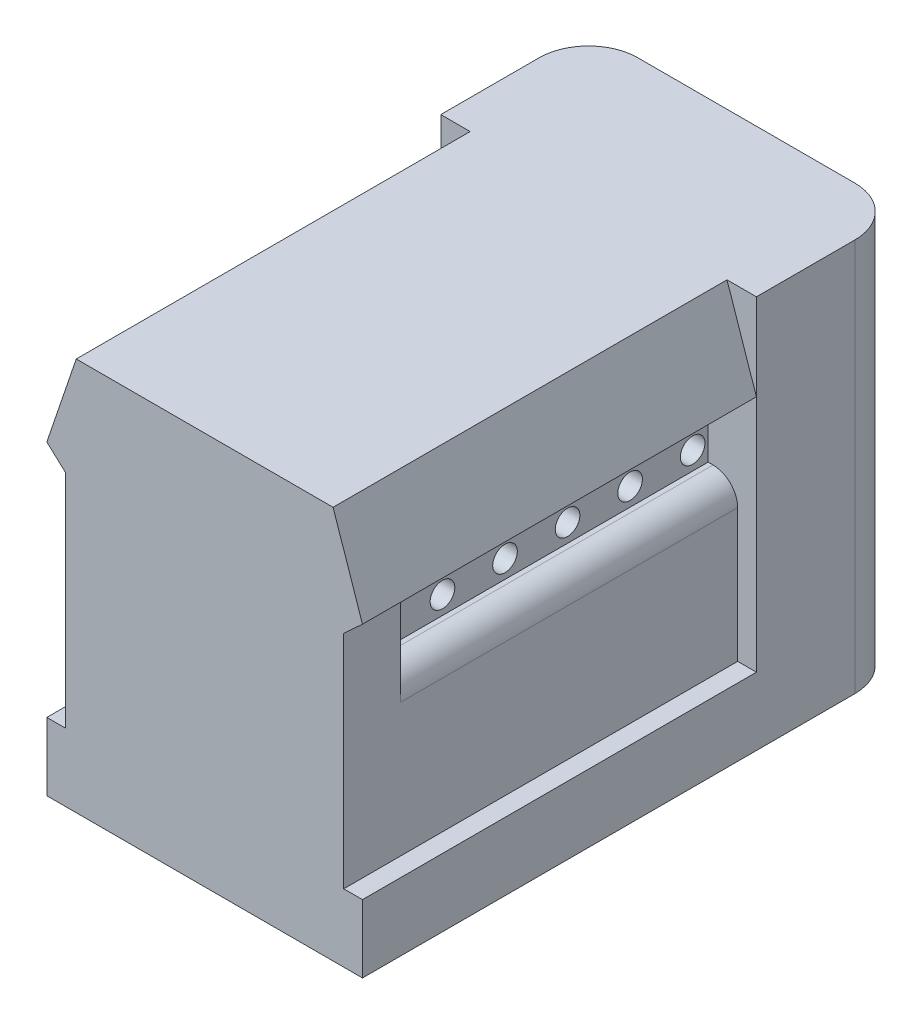
SolidWorks part; units mm, degrees
ref_plane "Plan de face" through (0, 0, 0) normal (0, 0, 1) x (1, 0, 0)
ref_plane "Plan de dessus" through (0, 0, 0) normal (0, 1, 0) x (1, 0, 0)
ref_plane "Plan de droite" through (0, 0, 0) normal (1, 0, 0) x (0, 0, -1)
sketch "Esquisse1" plane through (0, 0, 0) normal (0, 0, 1) x (1, 0, 0)
  line L0 (0, 0) -> (0, 63.4039) construction
  line L1 (-4.4493, 10.641) -> (-4.4493, 9.1647)
  line L2 (-6.41, 0) -> (-6.41, 2.7566)
  line L3 (-6.41, 2.7566) -> (-5.6493, 2.7566)
  line L4 (-4.4493, 9.1647) -> (-4.6493, 9.1647)
  line L5 (-4.4493, 10.641) -> (-6.41, 12.4442)
  line L6 (-6.41, 12.4442) -> (-5.2156, 15.9609)
  line L7 (-5.6493, 8.1647) -> (-5.6493, 2.7566)
  line L8 (-5.2156, 15.9609) -> (5.2156, 15.9609)
  line L9 (0, 0) -> (-6.41, 0)
  line L10 (5.6493, 8.1647) -> (5.6493, 2.7566)
  line L11 (6.41, 12.4442) -> (5.2156, 15.9609)
  line L12 (4.4493, 10.641) -> (6.41, 12.4442)
  line L13 (4.4493, 9.1647) -> (4.6493, 9.1647)
  line L14 (6.41, 2.7566) -> (5.6493, 2.7566)
  line L15 (6.41, 0) -> (6.41, 2.7566)
  line L16 (4.4493, 10.641) -> (4.4493, 9.1647)
  line L17 (0, 0) -> (6.41, 0)
  arc A0 (-4.6493, 9.1647) -> (-5.6493, 8.1647) centre (-4.6493, 8.1647) ccw
  arc A1 (4.6493, 9.1647) -> (5.6493, 8.1647) centre (4.6493, 8.1647) cw
  point P14 (-5.6493, 9.1647)
  point P20 (0, 15.9609)
  dimension "D2" = 1
  dimension "D1" = 1.2
  dimension "D3" = 0.7607
  dimension "D4" = 5.4081
  dimension "D5" = 1.4763
  dimension "D6" = 1.8032
  dimension "D7" = 132.604
  dimension "D8" = 3.714
  dimension "D9" = 113.845
  dimension "D10" = 6.41
extrude "Extrusion1" add sketch "Esquisse1" along normal blind 16
ref_plane "Plan1" through (6.41, 0, 0) normal (1, 0, 0) x (0, 0, -1)
sketch "Esquisse2" plane through (0, 15.9609, 0) normal (0, 1, 0) x (1, 0, 0)
  line L0 (0, 0) -> (0, 6.3868) construction
  line L1 (5.2156, 0) -> (-5.2156, 0) construction
  line L2 (6.41, -7.9805) -> (6.41, 7.9805) construction
  line L4 (-6.41, 0) -> (6.41, 0)
  line L5 (-6.41, 0) -> (-6.41, 4)
  line L6 (-4.41, 6) -> (4.41, 6)
  line L7 (6.41, 0) -> (6.41, 4)
  arc A0 (4.41, 6) -> (6.41, 4) centre (4.41, 4) cw
  arc A1 (-4.41, 6) -> (-6.41, 4) centre (-4.41, 4) ccw
  point P15 (0, 6)
  dimension "D2" = 2
  dimension "D1" = 6
extrude "Boss.-Extru.1" add sketch "Esquisse2" against normal up to surface (15.9609 mm away) up to face at (0, 0, 8)
sketch "Esquisse3" plane through (-4.4493, 0, 0) normal (-1, 0, 0) x (0, 0, 1)
  line L1 (-6, 0) -> (-6, 15.9609) construction
  circle A0 centre (0.63, 9.9028) radius 0.5
  dimension "D1" = 1
  dimension "D3" = 6.63
extrude "Enlèv. mat.-Extru.1" cut sketch "Esquisse3" against normal up to next (10.0986 mm away)
pattern_linear "Répétition linéaire1" count 5 spacing 2.54 along (0, 0, 1) of "Enlèv. mat.-Extru.1"
sketch "Esquisse4" plane through (0, 0, 0) normal (0, -1, 0) x (1, 0, 0)
  line L0 (-6.41, 16) -> (6.41, 16) construction
  line L1 (-5.3951, 16) -> (5.0141, 16)
  line L2 (-5.3951, 16) -> (-5.3951, 13.7)
  line L3 (-5.3951, 13.7) -> (5.0141, 13.7)
  line L4 (5.0141, 16) -> (5.0141, 13.7)
  dimension "D1" = 2.3
extrude "Boss.-Extru.2" add sketch "Esquisse4" against normal blind 13
sketch "Esquisse5" plane through (0, 0, 16) normal (0, 0, 1) x (1, 0, 0)
  line L0 (-5.6493, 2.7566) -> (-5.6493, 0) construction
  line L1 (-6.41, 0) -> (6.41, 0) construction
  line L2 (5.6493, 2.7566) -> (5.6493, 0) construction
sketch "Esquisse7" plane through (0, 0, 0) normal (0, -1, 0) x (1, 0, 0)
  line L1 (-5.6493, 16) -> (5.6493, 16)
  line L2 (-5.6493, 16) -> (-5.6493, 13.7)
  line L3 (-5.6493, 13.7) -> (5.6493, 13.7)
  line L4 (5.6493, 16) -> (5.6493, 13.7)
  dimension "D1" = 2.3
extrude "Boss.-Extru.3" add sketch "Esquisse7" against normal blind 13
sketch "Esquisse8" plane through (0, 0, 0) normal (0, -1, 0) x (1, 0, 0)
  line L0 (-5.1597, -4.45) -> (5.1444, -4.45) construction
  line L1 (-4.41, -6) -> (4.41, -6) construction
  line L2 (0, -6) -> (0, -2.0663) construction
  circle A0 centre (-0.0076, -4.45) radius 0.4
  circle A1 centre (-2.5476, -4.45) radius 0.4
  circle A2 centre (2.5476, -4.45) radius 0.4
  dimension "D2" = 0.8
  dimension "D3" = 0.8
  dimension "D1" = 1.55
  dimension "D4" = 2.54
extrude "Boss.-Extru.4" add sketch "Esquisse8" along normal blind 3
